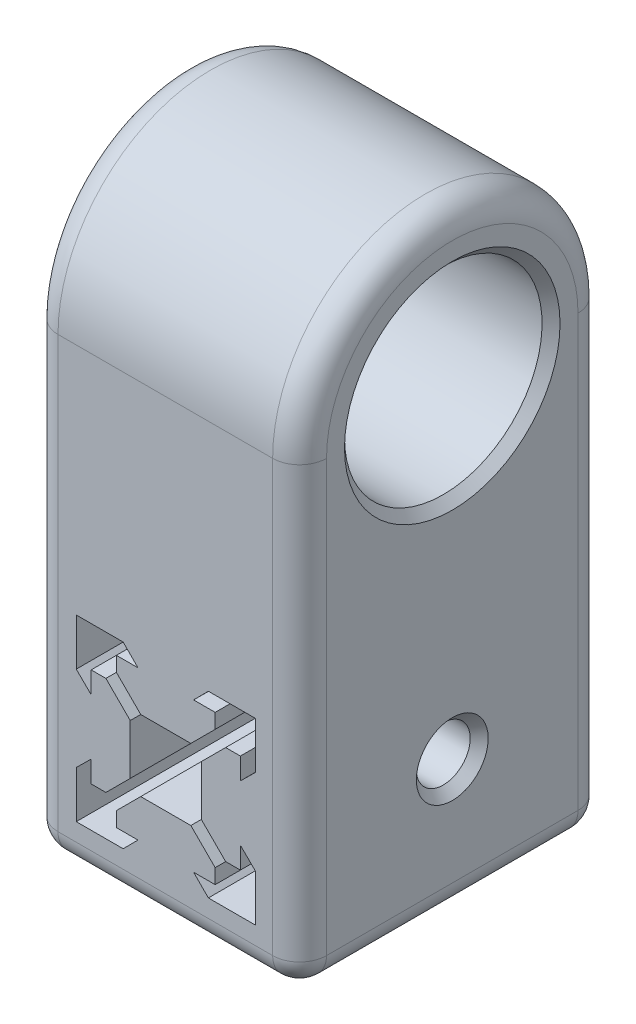
SolidWorks part; units mm, degrees
ref_plane "Front Plane" through (0, 0, 0) normal (0, 0, 1) x (1, 0, 0)
ref_plane "Top Plane" through (0, 0, 0) normal (0, 1, 0) x (1, 0, 0)
ref_plane "Right Plane" through (0, 0, 0) normal (1, 0, 0) x (0, 0, -1)
sketch "Sketch1" plane through (0, 0, 0) normal (0, 0, 1) x (1, 0, 0)
  line L0 (0, -15) -> (0, 15) construction
  line L1 (0, 15) -> (14.8993, 15)
  line L2 (14.8993, 15) -> (14.8993, -14.9496)
  line L3 (14.8993, -14.9496) -> (-15, -14.9496)
  line L4 (-15, -14.9496) -> (-15, 15)
  line L5 (-15, 15) -> (0, 15)
  line L6 (0, -9.9664) -> (0, 9.9664) construction
  line L7 (0, 9.9664) -> (-9.9664, 9.9664) construction
  line L8 (-9.9664, 9.9664) -> (-4.7414, 9.9664)
  line L9 (-4.7414, 9.9664) -> (-3.1, 8.3075)
  line L10 (-3.1, 8.3075) -> (0, 8.3075) construction
  line L11 (-3.1, 8.3075) -> (-5.5, 8.3075)
  line L12 (-5.5, 8.3075) -> (-5.5, 6.6675)
  line L13 (-5.5, 6.6675) -> (-2.79, 3.9575)
  line L14 (-2.79, 3.9575) -> (0, 3.9575) construction
  line L15 (-2.79, 3.9575) -> (2.79, 3.9575)
  line L16 (-9.9664, 9.9664) -> (0, 0) construction
  line L17 (-3.9575, 2.79) -> (-3.9575, -2.79)
  line L18 (-6.6675, 5.5) -> (-3.9575, 2.79)
  line L19 (-8.3075, 5.5) -> (-6.6675, 5.5)
  line L20 (-8.3075, 3.1) -> (-8.3075, 5.5)
  line L21 (-9.9664, 4.7414) -> (-8.3075, 3.1)
  line L22 (-9.9664, 9.9664) -> (-9.9664, 4.7414)
  line L23 (0, 0) -> (-11.0308, 0) construction
  line L24 (5.5, 6.6675) -> (2.79, 3.9575)
  line L25 (5.5, 8.3075) -> (5.5, 6.6675)
  line L26 (3.1, 8.3075) -> (5.5, 8.3075)
  line L27 (4.7414, 9.9664) -> (3.1, 8.3075)
  line L28 (9.9664, 9.9664) -> (4.7414, 9.9664)
  line L29 (9.9664, 9.9664) -> (9.9664, 4.7414)
  line L30 (9.9664, 4.7414) -> (8.3075, 3.1)
  line L31 (8.3075, 3.1) -> (8.3075, 5.5)
  line L32 (8.3075, 5.5) -> (6.6675, 5.5)
  line L33 (6.6675, 5.5) -> (3.9575, 2.79)
  line L34 (3.9575, 2.79) -> (3.9575, -2.79)
  line L35 (-9.9664, -9.9664) -> (0, 0) construction
  line L36 (-2.79, -3.9575) -> (0, -3.9575) construction
  line L37 (-3.1, -8.3075) -> (0, -8.3075) construction
  line L38 (0, -9.9664) -> (-9.9664, -9.9664) construction
  line L39 (6.6675, -5.5) -> (3.9575, -2.79)
  line L40 (8.3075, -5.5) -> (6.6675, -5.5)
  line L41 (8.3075, -3.1) -> (8.3075, -5.5)
  line L42 (9.9664, -4.7414) -> (8.3075, -3.1)
  line L43 (9.9664, -9.9664) -> (9.9664, -4.7414)
  line L44 (9.9664, -9.9664) -> (4.7414, -9.9664)
  line L45 (4.7414, -9.9664) -> (3.1, -8.3075)
  line L46 (3.1, -8.3075) -> (5.5, -8.3075)
  line L47 (5.5, -8.3075) -> (5.5, -6.6675)
  line L48 (5.5, -6.6675) -> (2.79, -3.9575)
  line L49 (-9.9664, -9.9664) -> (-9.9664, -4.7414)
  line L50 (-9.9664, -4.7414) -> (-8.3075, -3.1)
  line L51 (-8.3075, -3.1) -> (-8.3075, -5.5)
  line L52 (-8.3075, -5.5) -> (-6.6675, -5.5)
  line L53 (-6.6675, -5.5) -> (-3.9575, -2.79)
  line L54 (-2.79, -3.9575) -> (2.79, -3.9575)
  line L55 (-5.5, -6.6675) -> (-2.79, -3.9575)
  line L56 (-5.5, -8.3075) -> (-5.5, -6.6675)
  line L57 (-3.1, -8.3075) -> (-5.5, -8.3075)
  line L58 (-4.7414, -9.9664) -> (-3.1, -8.3075)
  line L59 (-9.9664, -9.9664) -> (-4.7414, -9.9664)
  point P43 (3.9575, 0)
  point P58 (-3.9575, 0)
  dimension "D1" = 3.1
  dimension "D2" = 2.79
  dimension "D3" = 2.4
  dimension "D4" = 135
  dimension "D5" = 1.64
  dimension "D6" = 15
  dimension "D7" = 15
  dimension "D8" = 9.9664
  dimension "D9" = 5.225
extrude "Boss-Extrude1" add sketch "Sketch1" along normal blind 34
sketch "Sketch5" plane through (-15, 0, 0) normal (-1, 0, 0) x (0, 0, 1)
  line L3 (0, 36) -> (0, 15)
  line L12 (0, 15) -> (0, -14.9496) construction
  line L13 (0, 12.8757) -> (34, 12.8757)
  line L14 (34, 15) -> (34, -14.9496) construction
  line L16 (0, 15) -> (0, 12.8757)
  line L17 (34, 12.8757) -> (34, 36)
  arc A0 (0, 36) -> (34, 36) centre (17, 36) cw
  circle A4 centre (17, 36) radius 11
  dimension "D3" = 21
extrude "Boss-Extrude3" add sketch "Sketch5" against normal through all
sketch "Sketch3" plane through (-15, 0, 0) normal (-1, 0, 0) x (0, 0, 1)
  line L2 (0, 0) -> (17, 0) construction
  circle A0 centre (17, 0) radius 3
extrude "Cut-Extrude1" cut sketch "Sketch3" against normal through all
fillet "Fillet1" radius 3 10 edges at (-15, 53, 17) (14.8993, 53, 17) (-0.0504, -14.9496, 34) (14.8993, 10.5252, 34) (-15, 10.5252, 34) (14.8993, 10.5252, 0) (-15, 10.5252, 0) (-0.0504, -14.9496, 0) (14.8993, -14.9496, 17) (-15, -14.9496, 17)
chamfer "Chamfer1" distance 1 angle 45 4 edges at (14.8993, 0, 20) (-15, 0, 20) (14.8993, 36, 28) (-15, 36, 28)
